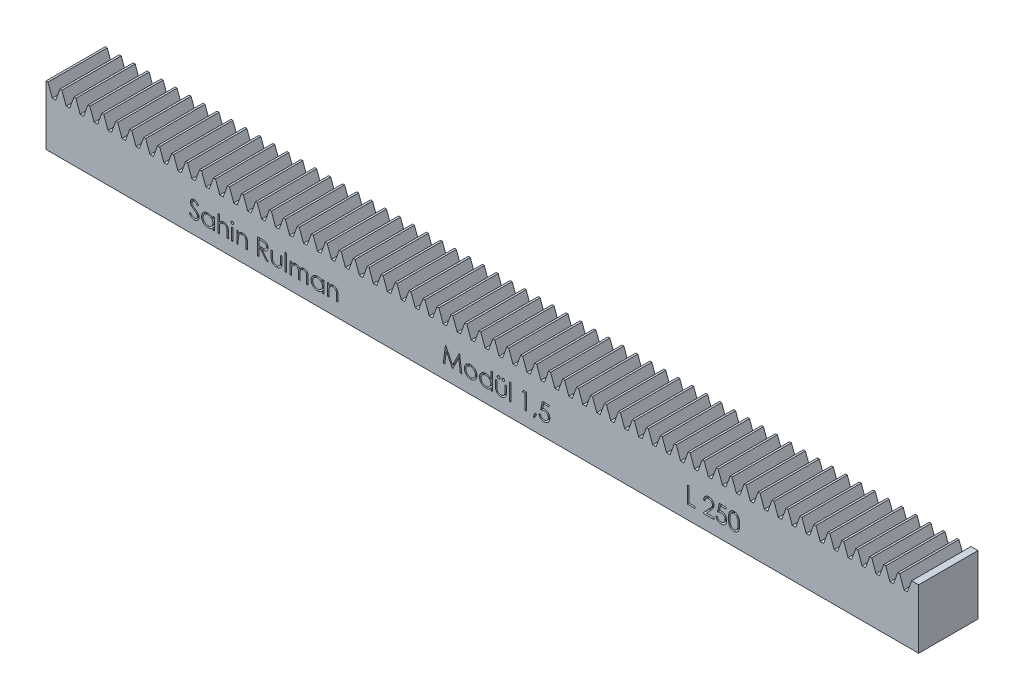
SolidWorks part; units mm, degrees
ref_plane "Front Plane" through (0, 0, 0) normal (0, 0, 1) x (1, 0, 0)
ref_plane "Top Plane" through (0, 0, 0) normal (0, 1, 0) x (1, 0, 0)
ref_plane "Right Plane" through (0, 0, 0) normal (1, 0, 0) x (0, 0, -1)
sketch "Sketch1" plane through (0, 0, 0) normal (1, 0, 0) x (0, 0, -1)
  line L1 (8.5, -8.5) -> (-8.5, -8.5)
  line L2 (8.5, -8.5) -> (8.5, 8.5)
  line L3 (8.5, 8.5) -> (-8.5, 8.5)
  line L4 (-8.5, -8.5) -> (-8.5, 8.5)
  line L5 (8.5, -8.5) -> (-8.5, 8.5) construction
  line L6 (8.5, 8.5) -> (-8.5, -8.5) construction
  point P0 (0, 0)
  dimension "D1" = 17
  dimension "D2" = 17
extrude "Boss-Extrude1" add sketch "Sketch1" along normal mid plane 250
sketch "Sketch2" plane through (0, 0, 8.5) normal (0, 0, 1) x (1, 0, 0)
  line L1 (119.5522, 8.5) -> (120.7806, 5.125)
  line L2 (125, 8.5) -> (-125, 8.5) construction
  line L3 (120.7806, 5.125) -> (121.7716, 5.125)
  line L4 (121.7716, 5.125) -> (123, 8.5)
  line L5 (119.5522, 8.5) -> (123, 8.5)
  dimension "D1" = 3.375
  dimension "D2" = 0.991
  dimension "D3" = 2
extrude "Cut-Extrude1" cut sketch "Sketch2" against normal through all
pattern_linear "LPattern1" count 124 spacing 4 along (-1, 0, 0) of "Cut-Extrude1"
sketch "Sketch3" plane through (0, 0, 8.5) normal (0, 0, 1) x (1, 0, 0)
  text T0 "Sahin Rulman                Modül 1,5                     L 250" font "Century Gothic" height in points 18
extrude "Cut-Extrude2" cut sketch "Sketch3" against normal blind 2
